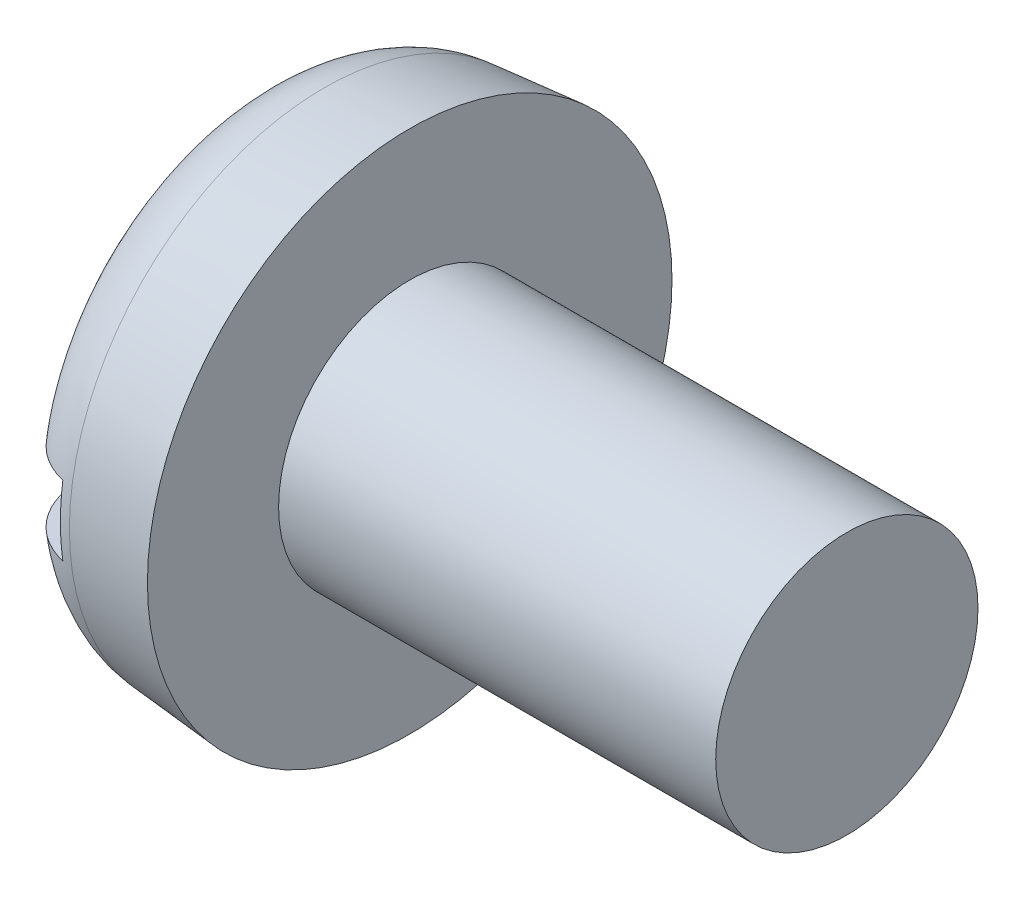
SolidWorks part; units mm, degrees
ref_plane "Plane1" through (0, 0, 0) normal (0, 0, 1) x (1, 0, 0)
ref_plane "Plane2" through (0, 0, 0) normal (0, 1, 0) x (1, 0, 0)
ref_plane "Plane3" through (0, 0, 0) normal (1, 0, 0) x (0, 0, -1)
sketch "BodySke" plane through (0, 0, 0) normal (0, 0, 1) x (1, 0, 0)
  line L0 (3.6, 3) -> (3.6, 6)
  line L1 (0, 0) -> (0, 5.685)
  line L2 (-25.4, 0) -> (127, 0) construction
  line L3 (13.6, 0) -> (0, 0)
  line L4 (3.6, 3) -> (13.6, 3)
  line L5 (13.6, 3) -> (13.6, 0)
  line L6 (0, 5.685) -> (3.6, 6)
  line L9 (4.6, 4.5875) -> (4.6, -4.9375) construction
  line L10 (3.6, 6.35) -> (3.6, -3.175) construction
  dimension "Head_ht" = 3.6
  dimension "Diameter" = 6
  dimension "Length" = 10
  dimension "Head_dia" = 12
  dimension "Advance" = 1
  dimension "Thread_nom" = 10
  dimension "Head_side_angle" = 5
revolve "Base-Revolve" add sketch "BodySke"
cosmetic thread "ThreadCosmetic"
fillet "Fillet1" [suppressed] radius 0.25
fillet "Fillet2" radius 1.8 1 edges at (0, 0, 5.685)
sketch "Sketch2" plane through (0, 0, 0) normal (1, 0, 0) x (0, 0, -1)
  line L0 (6, -0.8) -> (-6, -0.8)
  line L1 (6, -0.8) -> (6, 0.8)
  line L2 (-6, 0.8) -> (6, 0.8)
  line L3 (-6, 0.8) -> (-6, -0.8)
  dimension "D1" = 12
  dimension "D2" = 6
  dimension "Slot_width" = 1.6
  dimension "D3" = 0.8
extrude "Slot" cut sketch "Sketch2" along normal blind 1.4
sketch "ThdSchSke" plane through (0, 0, 0) normal (0, 0, 1) x (1, 0, 0)
  line L0 (5.6, -2.4455) -> (5.2117, -3)
  line L1 (5.6, -2.4455) -> (5.9883, -3)
  line L2 (5.9883, -3) -> (5.9883, -3.75)
  line L3 (-3.175, 0) -> (5.1513, 0) construction
  line L5 (5.9883, -3.75) -> (5.2117, -3.75)
  line L6 (5.2117, -3.75) -> (5.2117, -3)
  dimension "Thread_minor" = 4.891
  dimension "Diameter" = 6
  dimension "Start" = 5.6
  dimension "SideAngle" = 55
  dimension "VeeAngle" = 70
  dimension "Overcut" = 7.5
revolve "ThreadSchematic" [suppressed] cut sketch "ThdSchSke" angle 360 about L3
pattern_linear "ThdSchPat" [suppressed]
equation "\"D1@Sketch2\" = \"Head_dia@BodySke\""
equation "\"D2@Sketch2\" = \"D1@Sketch2\" / 2"
equation "\"D3@Sketch2\" = \"Slot_width@Sketch2\" / 2"
equation "\"Thread_length@ThreadCosmetic\" = ((sgn( (\"Length@BodySke\" - \"Advance@BodySke\" * 2.0 ) - \"Thread_nom@BodySke\" )-1)*( (\"Length@BodySke\" - \"Advance@BodySke\"  * 2.0) - \"Thread_nom@BodySke\" ))/-2+ \"Thread_nom@BodySke\""
equation "\"Thread_minor@ThdSchSke\" = \"Thread_minor@ThreadCosmetic\""
equation "\"Diameter@ThdSchSke\" = \"Diameter@BodySke\""
equation "\"Overcut@ThdSchSke\" = \"Diameter@BodySke\" * 1.25"
equation "\"Start@ThdSchSke\" = \"Head_ht@BodySke\" + \"Length@BodySke\" - \"Thread_length@ThreadCosmetic\"  '---Non-countersunk---"
equation "\"Num_threads@ThdSchPat\" = int( \"Thread_length@ThreadCosmetic\" / \"Advance@BodySke\" + 0.999 )  + 1"
equation "\"Advance@ThdSchPat\" = \"Thread_length@ThreadCosmetic\" /  (\"Num_threads@ThdSchPat\" - 1) 'relax it"
